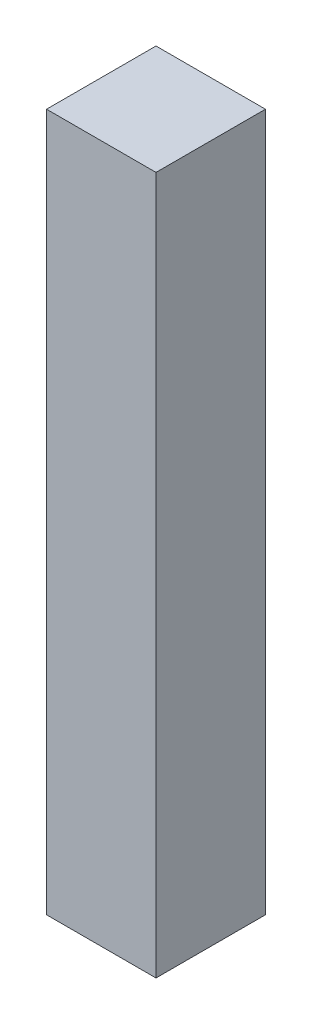
SolidWorks part; units mm, degrees
ref_plane "Front Plane" through (0, 0, 0) normal (0, 0, 1) x (1, 0, 0)
ref_plane "Top Plane" through (0, 0, 0) normal (0, 1, 0) x (1, 0, 0)
ref_plane "Right Plane" through (0, 0, 0) normal (1, 0, 0) x (0, 0, -1)
sketch "Sketch1" plane through (0, 0, 0) normal (0, 1, 0) x (1, 0, 0)
  line L1 (-12.7, -12.7) -> (12.7, -12.7)
  line L2 (-12.7, -12.7) -> (-12.7, 12.7)
  line L3 (-12.7, 12.7) -> (12.7, 12.7)
  line L4 (12.7, -12.7) -> (12.7, 12.7)
  line L5 (-12.7, -12.7) -> (12.7, 12.7) construction
  line L6 (-12.7, 12.7) -> (12.7, -12.7) construction
  point P0 (0, 0)
  dimension "D1" = 25.4
extrude "Boss-Extrude1" add sketch "Sketch1" along normal blind 161.9
